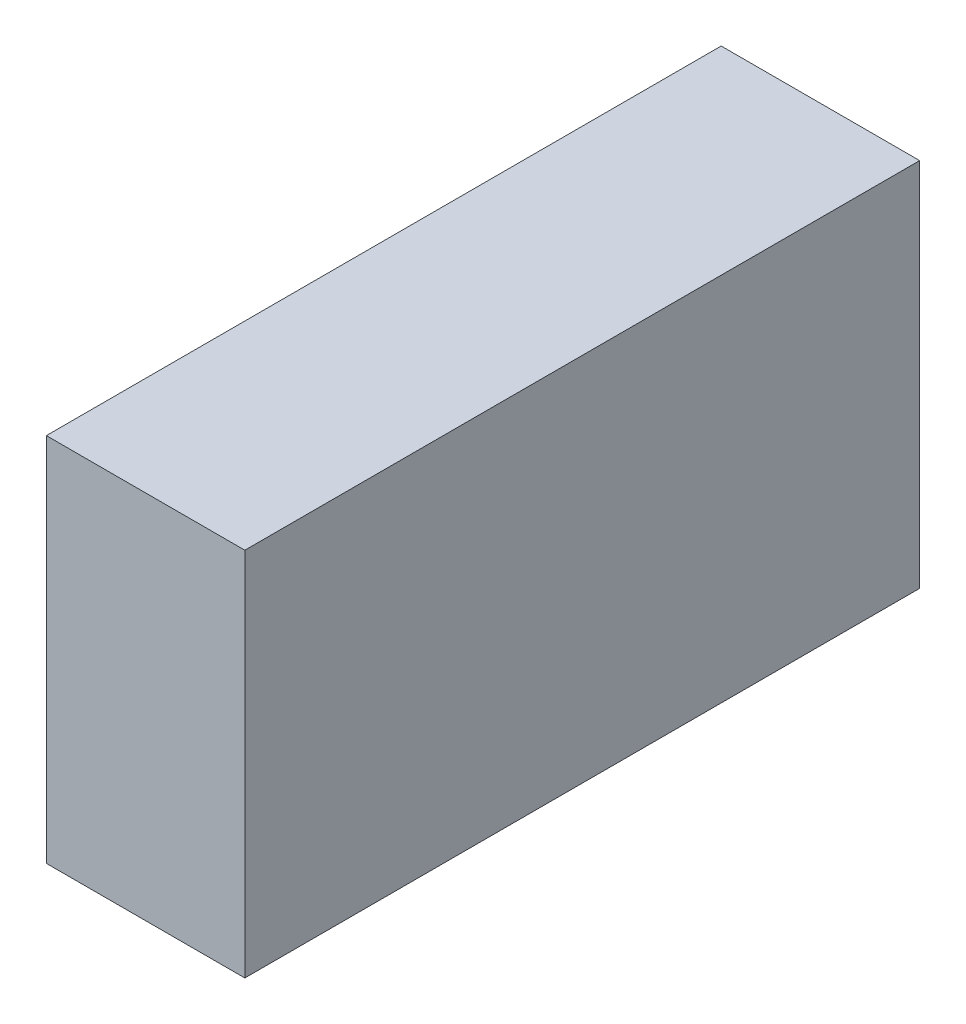
SolidWorks part; units mm, degrees
ref_plane "Płaszczyzna przednia" through (0, 0, 0) normal (0, 0, 1) x (1, 0, 0)
ref_plane "Płaszczyzna górna" through (0, 0, 0) normal (0, 1, 0) x (1, 0, 0)
ref_plane "Płaszczyzna prawa" through (0, 0, 0) normal (1, 0, 0) x (0, 0, -1)
sketch "Sketch1" plane through (0, 0, 0) normal (0, 1, 0) x (1, 0, 0)
  line L1 (-7.5, -25.5) -> (7.5, -25.5)
  line L2 (-7.5, -25.5) -> (-7.5, 25.5)
  line L3 (-7.5, 25.5) -> (7.5, 25.5)
  line L4 (7.5, -25.5) -> (7.5, 25.5)
  line L5 (-7.5, -25.5) -> (7.5, 25.5) construction
  line L6 (-7.5, 25.5) -> (7.5, -25.5) construction
  point P0 (0, 0)
  dimension "D1" = 15
  dimension "D2" = 51
extrude "Boss-Extrude1" add sketch "Sketch1" along normal blind 28
